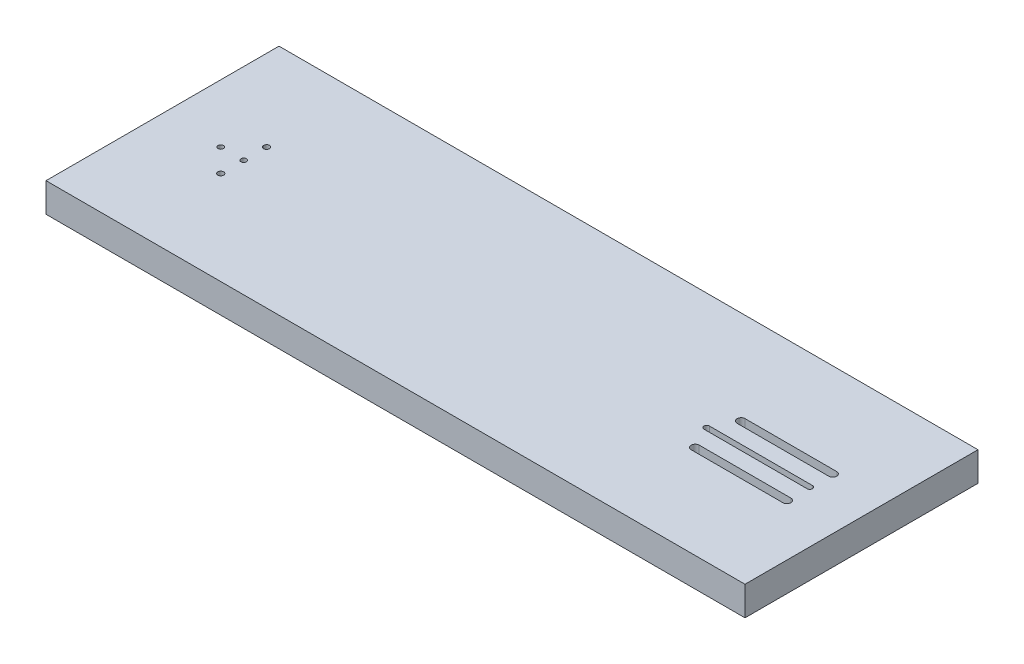
SolidWorks part; units mm, degrees
ref_plane "Front" through (0, 0, 0) normal (0, 0, 1) x (1, 0, 0)
ref_plane "Top" through (0, 0, 0) normal (0, 1, 0) x (1, 0, 0)
ref_plane "Right" through (0, 0, 0) normal (1, 0, 0) x (0, 0, -1)
sketch "Sketch1" plane through (0, 0, 0) normal (0, 1, 0) x (1, 0, 0)
  line L1 (0, 0) -> (609.6, 0)
  line L2 (0, 0) -> (0, 203.2)
  line L3 (0, 203.2) -> (609.6, 203.2)
  line L4 (609.6, 0) -> (609.6, 203.2)
extrude "Boss-Extrude1" add sketch "Sketch1" along normal blind 25.4
sketch "Sketch2" plane through (0, 25.4, 0) normal (0, 1, 0) x (1, 0, 0)
  line L0 (0, 101.6) -> (609.6, 101.6) construction
  line L1 (0, 203.2) -> (0, 0) construction
  line L2 (609.6, 0) -> (609.6, 203.2) construction
  line L3 (474.5309, 101.6) -> (564.5309, 101.6) construction
  line L4 (474.5309, 103.9815) -> (564.5309, 103.9815)
  line L5 (474.5309, 99.2185) -> (564.5309, 99.2185)
  line L6 (484.5413, 121.6) -> (564.5413, 121.6) construction
  line L7 (484.5413, 125.1) -> (564.5413, 125.1)
  line L8 (484.5413, 118.1) -> (564.5413, 118.1)
  line L9 (484.5413, 81.6) -> (564.5413, 81.6) construction
  line L10 (484.5413, 85.1) -> (564.5413, 85.1)
  line L11 (484.5413, 78.1) -> (564.5413, 78.1)
  circle A0 centre (50.8, 101.6) radius 2.3815
  circle A1 centre (70.8, 101.6) radius 2.3815
  circle A2 centre (70.8, 121.6) radius 2.5525
  circle A3 centre (70.8, 81.6) radius 2.5525
  arc A4 (474.5309, 103.9815) -> (474.5309, 99.2185) centre (474.5309, 101.6) ccw
  arc A5 (564.5309, 99.2185) -> (564.5309, 103.9815) centre (564.5309, 101.6) ccw
  arc A6 (484.5413, 125.1) -> (484.5413, 118.1) centre (484.5413, 121.6) ccw
  arc A7 (564.5413, 118.1) -> (564.5413, 125.1) centre (564.5413, 121.6) ccw
  arc A8 (484.5413, 85.1) -> (484.5413, 78.1) centre (484.5413, 81.6) ccw
  arc A9 (564.5413, 78.1) -> (564.5413, 85.1) centre (564.5413, 81.6) ccw
  point P17 (519.5309, 101.6)
  point P27 (524.5413, 121.6)
  point P32 (524.5413, 81.6)
  dimension "D1" = 20
  dimension "D2" = 20
  dimension "D3" = 20
  dimension "D7" = 50.8
extrude "Cut-Extrude2" cut sketch "Sketch2" against normal through all
sketch "Sketch7" plane through (0, 0, 0) normal (0, -1, 0) x (1, 0, 0)
  line L0 (484.5413, -81.6) -> (564.5413, -81.6) construction
  line L1 (484.5413, -76.1) -> (564.5413, -76.1)
  line L2 (484.5413, -87.1) -> (564.5413, -87.1)
  line L3 (484.5413, -121.6) -> (564.5413, -121.6) construction
  line L4 (484.5413, -116.1) -> (564.5413, -116.1)
  line L5 (484.5413, -127.1) -> (564.5413, -127.1)
  arc A0 (484.5413, -76.1) -> (484.5413, -87.1) centre (484.5413, -81.6) ccw
  arc A1 (564.5413, -87.1) -> (564.5413, -76.1) centre (564.5413, -81.6) ccw
  arc A2 (484.5413, -116.1) -> (484.5413, -127.1) centre (484.5413, -121.6) ccw
  arc A3 (564.5413, -127.1) -> (564.5413, -116.1) centre (564.5413, -121.6) ccw
  point P4 (524.5413, -81.6)
  point P13 (524.5413, -121.6)
extrude "Cut-Extrude3" cut sketch "Sketch7" against normal blind 8
